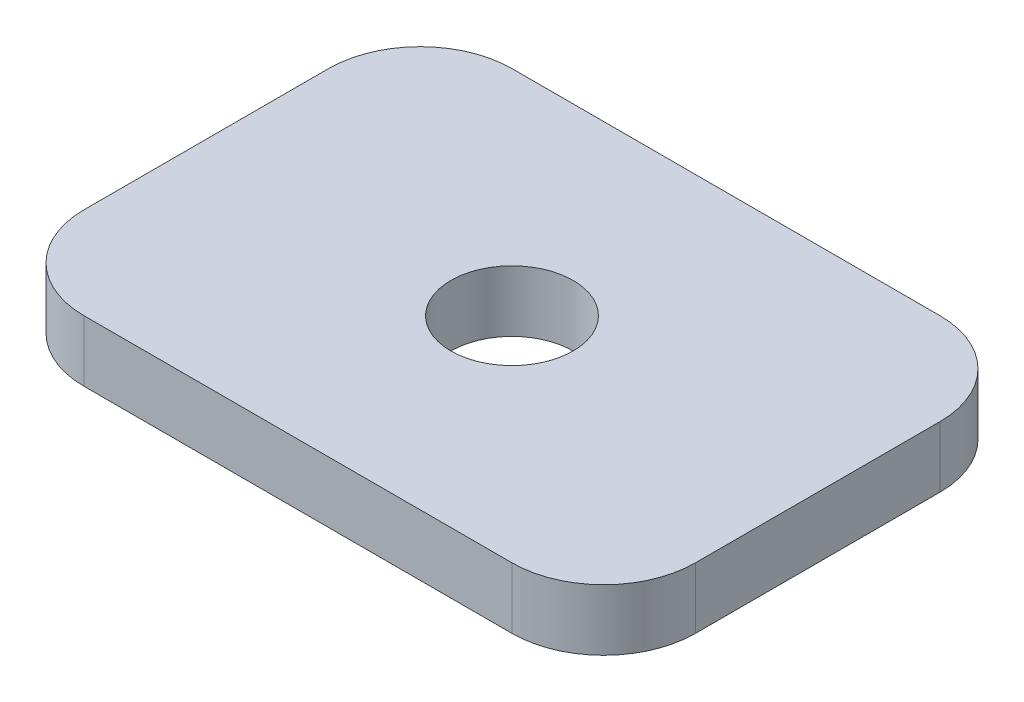
SolidWorks part; units mm, degrees
material "ABS"
ref_plane "Front Plane" through (0, 0, 0) normal (0, 0, 1) x (1, 0, 0)
ref_plane "Top Plane" through (0, 0, 0) normal (0, 1, 0) x (1, 0, 0)
ref_plane "Right Plane" through (0, 0, 0) normal (1, 0, 0) x (0, 0, -1)
sketch "Sketch1" plane through (0, 0, 0) normal (0, 1, 0) x (1, 0, 0)
  line L1 (50, -35) -> (-50, -35)
  line L2 (50, -35) -> (50, 35)
  line L3 (50, 35) -> (-50, 35)
  line L4 (-50, -35) -> (-50, 35)
  line L5 (50, -35) -> (-50, 35) construction
  line L6 (50, 35) -> (-50, -35) construction
  point P0 (0, 0)
  dimension "D1" = 100
  dimension "D2" = 70
extrude "Boss-Extrude1" add sketch "Sketch1" along normal blind 10
sketch "Sketch2" plane through (0, 10, 0) normal (0, 1, 0) x (1, 0, 0)
  circle A0 centre (0, 0) radius 10
  dimension "D1" = 20
extrude "Cut-Extrude1" cut sketch "Sketch2" against normal through all
fillet "Fillet1" [suppressed] radius 25.4
sketch "Sketch3" plane through (0, 0, 0) normal (0, -1, 0) x (1, 0, 0)
  line L0 (40, 0) -> (-40, 0) construction
  point P4 (0, 0)
  dimension "D1" = 80
sketch "Sketch4" plane through (0, 0, 0) normal (0, -1, 0) x (-1, 0, 0)
  point P0 (40, 0)
  point P3 (-40, 0)
hole_wizard "Ø3.0mm Dowel Hole1" positions "Sketch4" profile "Sketch5" hole size "Ø3.0" standard "ISO"
sketch "Sketch5" plane through (-40, 0, 0) normal (1, 0, 0) x (0, 0, -1)
  line L0 (0, 0) -> (0, 5.9013)
  line L1 (0, 5.9013) -> (1.5, 5)
  line L2 (1.5, 5) -> (1.5, 0)
  line L5 (1.5, 0) -> (0, 0)
  line L10 (0, 5.9013) -> (-1.5, 5) construction
  line L11 (0, -6.35) -> (0, 107.95) construction
  dimension "Hole Dia." = 3
  dimension "Hole Depth" = 5
  dimension "Drill Angle" = 118
fillet "Fillet2" radius 15 4 edges at (-50, 5, 35) (50, 5, 35) (50, 5, -35) (-50, 5, -35)
